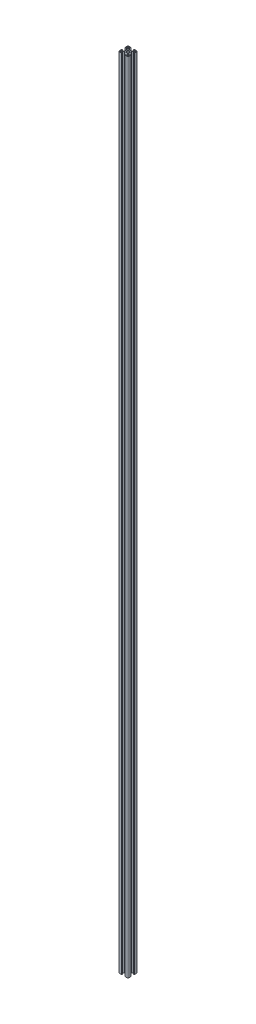
SolidWorks part; units mm, degrees
material "6063-T5"
ref_plane "前视基准面" through (0, 0, 0) normal (0, 0, 1) x (1, 0, 0)
ref_plane "上视基准面" through (0, 0, 0) normal (0, 1, 0) x (1, 0, 0)
ref_plane "右视基准面" through (0, 0, 0) normal (1, 0, 0) x (0, 0, -1)
sketch "草图3" plane through (0, 0, 0) normal (0, 1, 0) x (1, 0, 0)
  line L0 (0, 0) -> (-15, -15) construction
  line L1 (-15, -15) -> (-15, 0) construction
  line L2 (-15, 0) -> (0, 0) construction
  line L3 (-15, -12.5) -> (-15, -5.4)
  line L4 (-14.8, -5.2) -> (-14.4, -5.2)
  line L5 (-14.2, -5) -> (-14.2, -4.3)
  line L6 (-14, -4.1) -> (-13.2, -4.1)
  line L7 (-13.2, -4.1) -> (-13.2, -8.25)
  line L8 (-13.2, -8.25) -> (-9.5228, -8.25)
  line L9 (-9.5228, -8.25) -> (-5.8, -4.5272)
  line L10 (-5.8, -4.5272) -> (-5.8, 4.5272)
  line L11 (-13.2, -12.2) -> (-13.2, -11.05)
  line L12 (-12.2, -10.05) -> (-11.05, -10.05)
  line L13 (-4.5272, -5.8) -> (4.5272, -5.8)
  line L14 (-8.25, -9.5228) -> (-4.5272, -5.8)
  line L15 (-12.2, -13.2) -> (-11.05, -13.2)
  line L16 (-10.05, -12.2) -> (-10.05, -11.05)
  line L17 (-5.2, -14.8) -> (-5.2, -14.4)
  line L18 (-5, -14.2) -> (-4.3, -14.2)
  line L19 (-4.1, -14) -> (-4.1, -13.2)
  line L20 (-4.1, -13.2) -> (-8.25, -13.2)
  line L21 (-8.25, -13.2) -> (-8.25, -9.5228)
  line L22 (-12.5, -15) -> (-5.4, -15)
  line L23 (-12.5, 15) -> (-5.4, 15)
  line L24 (-8.25, 13.2) -> (-8.25, 9.5228)
  line L25 (-4.1, 13.2) -> (-8.25, 13.2)
  line L26 (-4.1, 14) -> (-4.1, 13.2)
  line L27 (-5, 14.2) -> (-4.3, 14.2)
  line L28 (-5.2, 14.8) -> (-5.2, 14.4)
  line L29 (-10.05, 12.2) -> (-10.05, 11.05)
  line L30 (-12.2, 13.2) -> (-11.05, 13.2)
  line L31 (-8.25, 9.5228) -> (-4.5272, 5.8)
  line L32 (-4.5272, 5.8) -> (4.5272, 5.8)
  line L33 (-12.2, 10.05) -> (-11.05, 10.05)
  line L34 (-13.2, 12.2) -> (-13.2, 11.05)
  line L35 (-9.5228, 8.25) -> (-5.8, 4.5272)
  line L36 (-13.2, 8.25) -> (-9.5228, 8.25)
  line L37 (-13.2, 4.1) -> (-13.2, 8.25)
  line L38 (-14, 4.1) -> (-13.2, 4.1)
  line L39 (-14.2, 5) -> (-14.2, 4.3)
  line L40 (-14.8, 5.2) -> (-14.4, 5.2)
  line L41 (-15, 12.5) -> (-15, 5.4)
  line L42 (0, 0) -> (0, -12.3268) construction
  line L43 (15, 12.5) -> (15, 5.4)
  line L44 (14.8, 5.2) -> (14.4, 5.2)
  line L45 (14.2, 5) -> (14.2, 4.3)
  line L46 (14, 4.1) -> (13.2, 4.1)
  line L47 (13.2, 4.1) -> (13.2, 8.25)
  line L48 (13.2, 8.25) -> (9.5228, 8.25)
  line L49 (9.5228, 8.25) -> (5.8, 4.5272)
  line L50 (13.2, 12.2) -> (13.2, 11.05)
  line L51 (12.2, 10.05) -> (11.05, 10.05)
  line L52 (8.25, 9.5228) -> (4.5272, 5.8)
  line L53 (12.2, 13.2) -> (11.05, 13.2)
  line L54 (10.05, 12.2) -> (10.05, 11.05)
  line L55 (5.2, 14.8) -> (5.2, 14.4)
  line L56 (5, 14.2) -> (4.3, 14.2)
  line L57 (4.1, 14) -> (4.1, 13.2)
  line L58 (4.1, 13.2) -> (8.25, 13.2)
  line L59 (8.25, 13.2) -> (8.25, 9.5228)
  line L60 (12.5, 15) -> (5.4, 15)
  line L61 (12.5, -15) -> (5.4, -15)
  line L62 (8.25, -13.2) -> (8.25, -9.5228)
  line L63 (4.1, -13.2) -> (8.25, -13.2)
  line L64 (4.1, -14) -> (4.1, -13.2)
  line L65 (5, -14.2) -> (4.3, -14.2)
  line L66 (5.2, -14.8) -> (5.2, -14.4)
  line L67 (10.05, -12.2) -> (10.05, -11.05)
  line L68 (12.2, -13.2) -> (11.05, -13.2)
  line L69 (8.25, -9.5228) -> (4.5272, -5.8)
  line L70 (12.2, -10.05) -> (11.05, -10.05)
  line L71 (13.2, -12.2) -> (13.2, -11.05)
  line L72 (5.8, -4.5272) -> (5.8, 4.5272)
  line L73 (9.5228, -8.25) -> (5.8, -4.5272)
  line L74 (13.2, -8.25) -> (9.5228, -8.25)
  line L75 (13.2, -4.1) -> (13.2, -8.25)
  line L76 (14, -4.1) -> (13.2, -4.1)
  line L77 (14.2, -5) -> (14.2, -4.3)
  line L78 (14.8, -5.2) -> (14.4, -5.2)
  line L79 (15, -12.5) -> (15, -5.4)
  circle A0 centre (0, 0) radius 3.4
  arc A1 (-12.5, 15) -> (-15, 12.5) centre (-12.5, 12.5) ccw
  arc A2 (15, 12.5) -> (12.5, 15) centre (12.5, 12.5) ccw
  arc A3 (12.5, -15) -> (15, -12.5) centre (12.5, -12.5) ccw
  arc A4 (-15, -12.5) -> (-12.5, -15) centre (-12.5, -12.5) ccw
  arc A5 (-12.2, 13.2) -> (-13.2, 12.2) centre (-12.2, 12.2) ccw
  arc A6 (-12.2, 10.05) -> (-13.2, 11.05) centre (-12.2, 11.05) cw
  arc A7 (-10.05, 11.05) -> (-11.05, 10.05) centre (-11.05, 11.05) cw
  arc A8 (-10.05, 12.2) -> (-11.05, 13.2) centre (-11.05, 12.2) ccw
  arc A9 (11.05, 10.05) -> (10.05, 11.05) centre (11.05, 11.05) cw
  arc A10 (11.05, 13.2) -> (10.05, 12.2) centre (11.05, 12.2) ccw
  arc A11 (13.2, 12.2) -> (12.2, 13.2) centre (12.2, 12.2) ccw
  arc A12 (13.2, 11.05) -> (12.2, 10.05) centre (12.2, 11.05) cw
  arc A13 (12.2, -10.05) -> (13.2, -11.05) centre (12.2, -11.05) cw
  arc A14 (10.05, -11.05) -> (11.05, -10.05) centre (11.05, -11.05) cw
  arc A15 (10.05, -12.2) -> (11.05, -13.2) centre (11.05, -12.2) ccw
  arc A16 (12.2, -13.2) -> (13.2, -12.2) centre (12.2, -12.2) ccw
  arc A17 (-13.2, -11.05) -> (-12.2, -10.05) centre (-12.2, -11.05) cw
  arc A18 (-11.05, -10.05) -> (-10.05, -11.05) centre (-11.05, -11.05) cw
  arc A19 (-11.05, -13.2) -> (-10.05, -12.2) centre (-11.05, -12.2) ccw
  arc A20 (-13.2, -12.2) -> (-12.2, -13.2) centre (-12.2, -12.2) ccw
  arc A21 (-15, -5.4) -> (-14.8, -5.2) centre (-14.8, -5.4) cw
  arc A22 (-14.4, -5.2) -> (-14.2, -5) centre (-14.4, -5) ccw
  arc A23 (-14.2, -4.3) -> (-14, -4.1) centre (-14, -4.3) cw
  arc A24 (-14, 4.1) -> (-14.2, 4.3) centre (-14, 4.3) cw
  arc A25 (-14.2, 5) -> (-14.4, 5.2) centre (-14.4, 5) ccw
  arc A26 (-14.8, 5.2) -> (-15, 5.4) centre (-14.8, 5.4) cw
  arc A27 (-5.4, 15) -> (-5.2, 14.8) centre (-5.4, 14.8) cw
  arc A28 (-5, 14.2) -> (-5.2, 14.4) centre (-5, 14.4) cw
  arc A29 (-4.1, 14) -> (-4.3, 14.2) centre (-4.3, 14) ccw
  arc A30 (5.2, 14.8) -> (5.4, 15) centre (5.4, 14.8) cw
  arc A31 (5.2, 14.4) -> (5, 14.2) centre (5, 14.4) cw
  arc A32 (4.3, 14.2) -> (4.1, 14) centre (4.3, 14) ccw
  arc A33 (15, 5.4) -> (14.8, 5.2) centre (14.8, 5.4) cw
  arc A34 (14.4, 5.2) -> (14.2, 5) centre (14.4, 5) ccw
  arc A35 (14.2, 4.3) -> (14, 4.1) centre (14, 4.3) cw
  arc A36 (14, -4.1) -> (14.2, -4.3) centre (14, -4.3) cw
  arc A37 (14.2, -5) -> (14.4, -5.2) centre (14.4, -5) ccw
  arc A38 (14.8, -5.2) -> (15, -5.4) centre (14.8, -5.4) cw
  arc A39 (5.4, -15) -> (5.2, -14.8) centre (5.4, -14.8) cw
  arc A40 (5, -14.2) -> (5.2, -14.4) centre (5, -14.4) cw
  arc A41 (4.1, -14) -> (4.3, -14.2) centre (4.3, -14) ccw
  arc A42 (-5.2, -14.4) -> (-5, -14.2) centre (-5, -14.4) cw
  arc A43 (-4.3, -14.2) -> (-4.1, -14) centre (-4.3, -14) ccw
  arc A44 (-5.2, -14.8) -> (-5.4, -15) centre (-5.4, -14.8) cw
  point P38 (-5.8, 0)
  point P46 (0, 5.8)
  point P47 (0, -5.8)
  point P83 (5.8, 0)
  point P87 (-15, 15)
  point P90 (15, 15)
  point P93 (15, -15)
  point P99 (-13.2, 13.2)
  point P102 (-13.2, 10.05)
  point P105 (-10.05, 10.05)
  point P108 (-10.05, 13.2)
  point P111 (10.05, 10.05)
  point P114 (10.05, 13.2)
  point P117 (13.2, 13.2)
  point P120 (13.2, 10.05)
  point P123 (13.2, -10.05)
  point P126 (10.05, -10.05)
  point P129 (10.05, -13.2)
  point P132 (13.2, -13.2)
  point P135 (-13.2, -10.05)
  point P138 (-10.05, -10.05)
  point P141 (-10.05, -13.2)
  point P144 (-13.2, -13.2)
  point P147 (-15, -5.2)
  point P150 (-14.2, -5.2)
  point P153 (-14.2, -4.1)
  point P156 (-14.2, 4.1)
  point P159 (-14.2, 5.2)
  point P162 (-15, 5.2)
  point P165 (-5.2, 15)
  point P168 (-5.2, 14.2)
  point P171 (-4.1, 14.2)
  point P174 (5.2, 15)
  point P177 (5.2, 14.2)
  point P180 (4.1, 14.2)
  point P183 (15, 5.2)
  point P186 (14.2, 5.2)
  point P189 (14.2, 4.1)
  point P192 (14.2, -4.1)
  point P195 (14.2, -5.2)
  point P198 (15, -5.2)
  point P201 (5.2, -15)
  point P204 (5.2, -14.2)
  point P207 (4.1, -14.2)
  point P210 (-5.2, -14.2)
  point P213 (-4.1, -14.2)
  point P216 (-5.2, -15)
  dimension "D11" = 6.8
  dimension "D12" = 2.5
  dimension "D13" = 1
  dimension "D14" = 0.2
  dimension "D2" = 15
  dimension "D3" = 4.1
  dimension "D4" = 5.2
  dimension "D5" = 0.8
  dimension "D6" = 1.8
  dimension "D7" = 9.2
  dimension "D8" = 8.25
  dimension "D9" = 0.9
  dimension "D10" = 1.8
extrude "凸台-拉伸1" add sketch "草图3" along normal blind 2488
